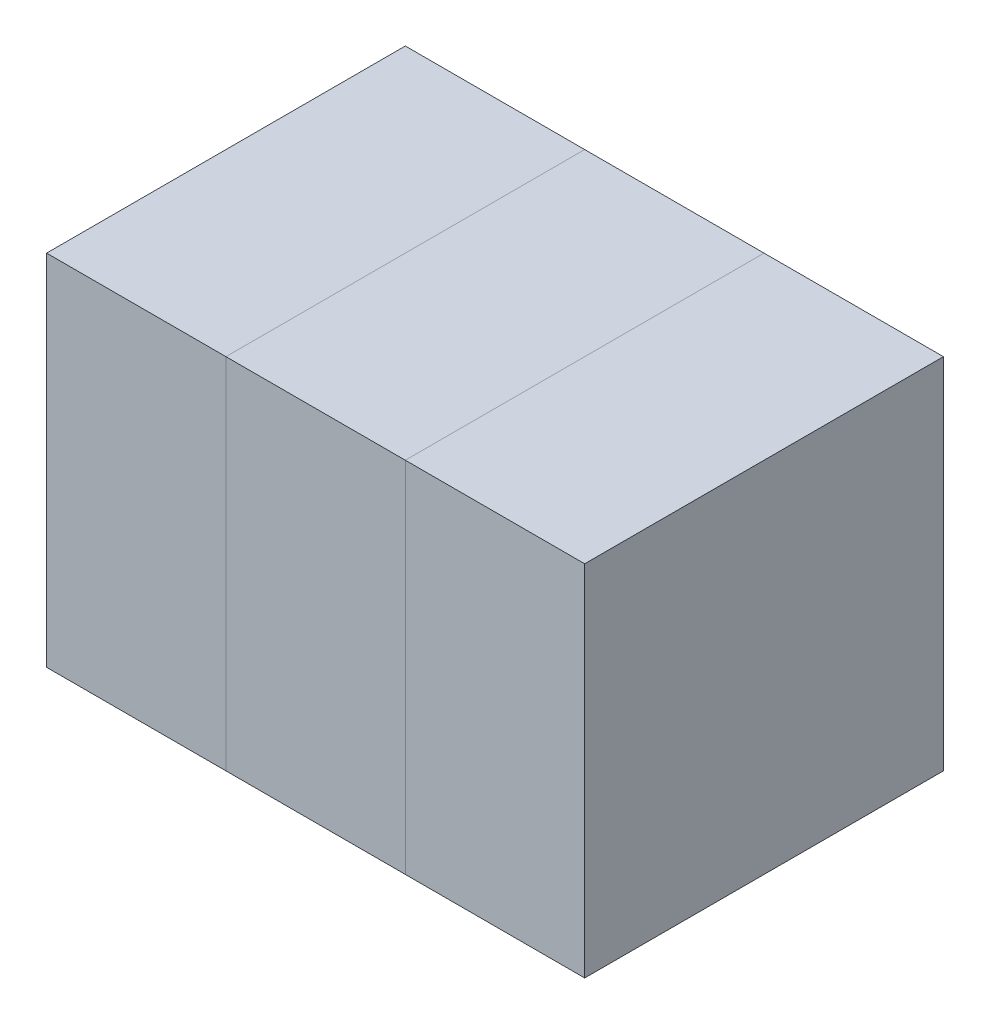
SolidWorks part; units mm, degrees
ref_plane "Front Plane" through (0, 0, 0) normal (0, 0, 1) x (1, 0, 0)
ref_plane "Top Plane" through (0, 0, 0) normal (0, 1, 0) x (1, 0, 0)
ref_plane "Right Plane" through (0, 0, 0) normal (1, 0, 0) x (0, 0, -1)
sketch "Sketch1" plane through (0, 0, 0) normal (0, 1, 0) x (1, 0, 0)
  line L1 (-0.2, -0.4) -> (0.2, -0.4)
  line L2 (-0.2, -0.4) -> (-0.2, 0.4)
  line L3 (-0.2, 0.4) -> (0.2, 0.4)
  line L4 (0.2, -0.4) -> (0.2, 0.4)
  line L5 (-0.2, -0.4) -> (0.2, 0.4) construction
  line L6 (-0.2, 0.4) -> (0.2, -0.4) construction
  point P0 (0, 0)
  dimension "D1" = 0.4
  dimension "D2" = 0.8
extrude "Boss-Extrude1" add sketch "Sketch1" along normal blind 0.8
sketch "Sketch2" plane through (0, 0, 0) normal (0, 1, 0) x (1, 0, 0)
  line L0 (0, 0.4) -> (0, -0.4) construction
  line L1 (-0.2, 0.4) -> (-0.6, 0.4)
  line L2 (-0.2, 0.4) -> (-0.2, -0.4)
  line L3 (-0.2, -0.4) -> (-0.6, -0.4)
  line L4 (-0.6, 0.4) -> (-0.6, -0.4)
  line L5 (0.2, 0.4) -> (-0.2, 0.4) construction
  line L6 (-0.2, -0.4) -> (0.2, -0.4) construction
  line L7 (0.2, -0.4) -> (0.6, -0.4)
  line L8 (0.6, 0.4) -> (0.6, -0.4)
  line L9 (0.2, 0.4) -> (0.6, 0.4)
  line L10 (0.2, 0.4) -> (0.2, -0.4)
  dimension "D1" = 0.8
  dimension "D2" = 0.4
extrude "Boss-Extrude2" add sketch "Sketch2" along normal blind 0.8 separate body
